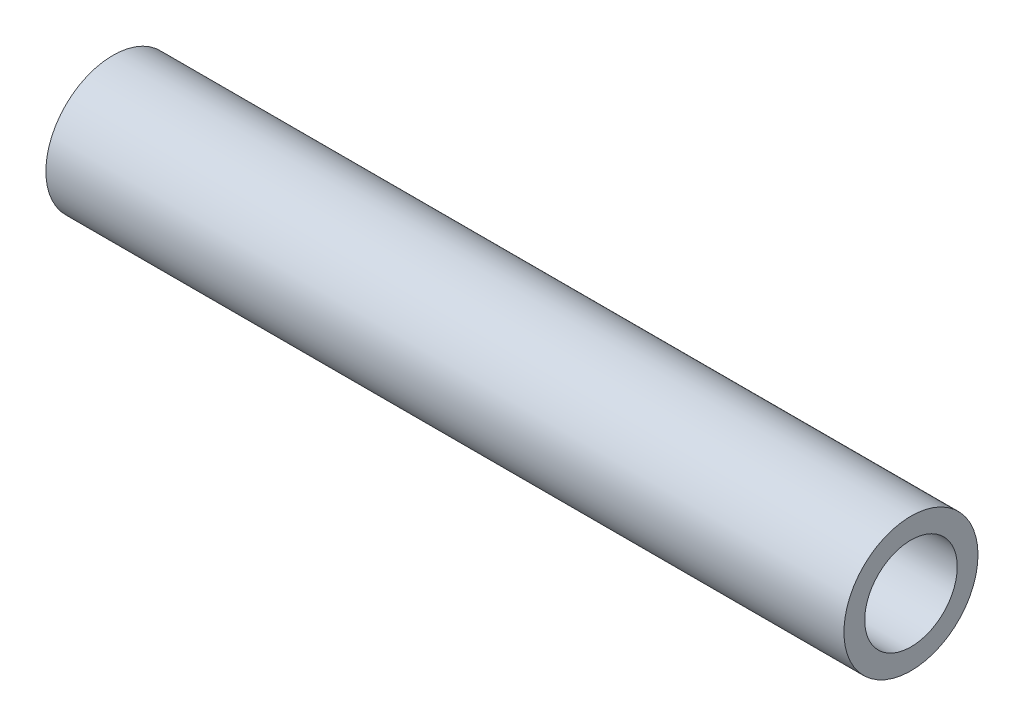
SolidWorks part; units mm, degrees
material "PVC 0.007 Plasticized"
ref_plane "Front Plane" through (0, 0, 0) normal (0, 0, 1) x (1, 0, 0)
ref_plane "Top Plane" through (0, 0, 0) normal (0, 1, 0) x (1, 0, 0)
ref_plane "Right Plane" through (0, 0, 0) normal (1, 0, 0) x (0, 0, -1)
sketch "Sketch1" plane through (0, 0, 0) normal (1, 0, 0) x (0, 0, -1)
  circle A0 centre (0, 0) radius 10.668
  circle A1 centre (0, 0) radius 7.366
  dimension "D1" = 21.336
  dimension "D2" = 14.732
extrude "Boss-Extrude1" add sketch "Sketch1" against normal blind 127
